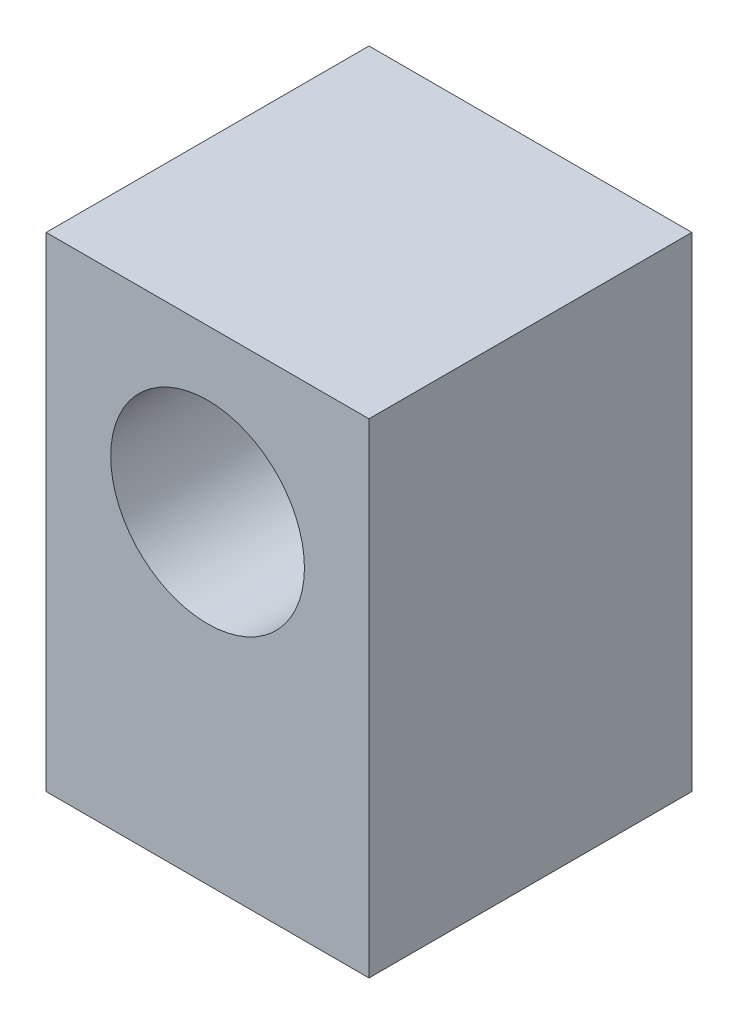
SolidWorks part; units mm, degrees
ref_plane "Front Plane" through (0, 0, 0) normal (0, 0, 1) x (1, 0, 0)
ref_plane "Top Plane" through (0, 0, 0) normal (0, 1, 0) x (1, 0, 0)
ref_plane "Right Plane" through (0, 0, 0) normal (1, 0, 0) x (0, 0, -1)
sketch "Sketch1" plane through (0, 0, 0) normal (0, 1, 0) x (1, 0, 0)
  line L1 (-10, 10) -> (10, 10)
  line L2 (-10, 10) -> (-10, -10)
  line L3 (-10, -10) -> (10, -10)
  line L4 (10, 10) -> (10, -10)
  line L5 (-10, 10) -> (10, -10) construction
  line L6 (-10, -10) -> (10, 10) construction
  point P0 (0, 0)
  dimension "D1" = 20
  dimension "20" = 20
extrude "Boss-Extrude2" add sketch "Sketch1" along normal blind 30
sketch "Sketch2" plane through (0, 0, 10) normal (0, 0, 1) x (1, 0, 0)
  circle A0 centre (0, 20) radius 6
extrude "Cut-Extrude1" cut sketch "Sketch2" against normal up to next
sketch "Sketch3" plane through (0, 0, 0) normal (0, -1, 0) x (1, 0, 0)
  circle A0 centre (0, 0) radius 5
extrude "Cut-Extrude2" cut sketch "Sketch3" against normal blind 8
